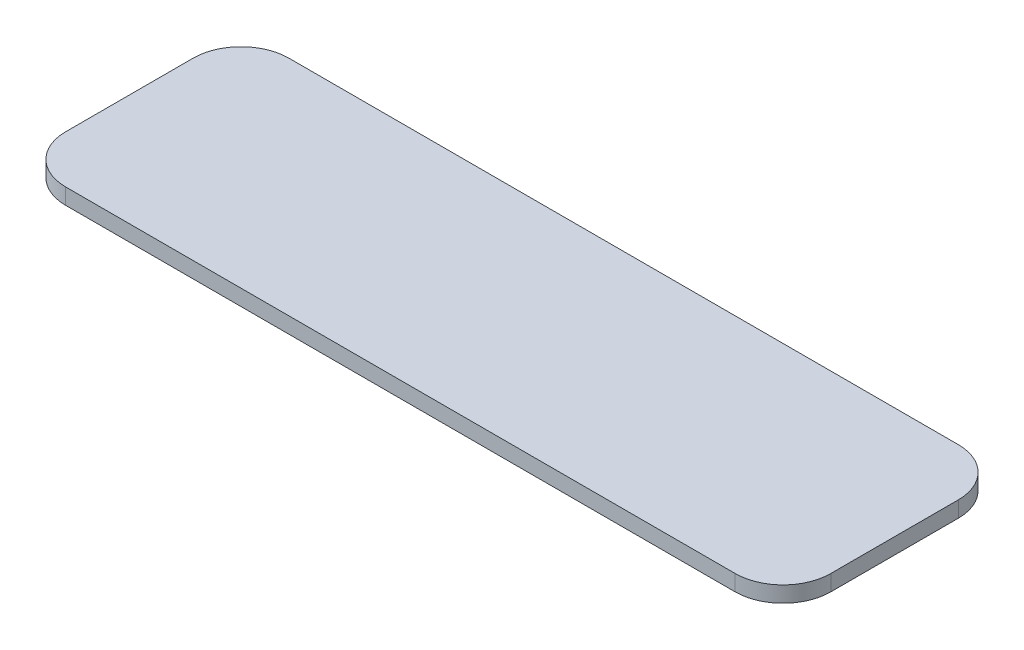
SolidWorks part; units mm, degrees
ref_plane "前视基准面" through (0, 0, 0) normal (0, 0, 1) x (1, 0, 0)
ref_plane "上视基准面" through (0, 0, 0) normal (0, 1, 0) x (1, 0, 0)
ref_plane "右视基准面" through (0, 0, 0) normal (1, 0, 0) x (0, 0, -1)
other "Configuration Table"
sketch "草图1" plane through (0, 0, 0) normal (0, 1, 0) x (1, 0, 0)
  line L1 (-31.5, 10.5) -> (31.5, 10.5)
  line L2 (-36, 6) -> (-36, -6)
  line L3 (-31.5, -10.5) -> (31.5, -10.5)
  line L4 (36, 6) -> (36, -6)
  line L5 (-36, 10.5) -> (36, -10.5) construction
  line L6 (-36, -10.5) -> (36, 10.5) construction
  arc A0 (31.5, 10.5) -> (36, 6) centre (31.5, 6) cw
  arc A1 (31.5, -10.5) -> (36, -6) centre (31.5, -6) ccw
  arc A2 (-36, -6) -> (-31.5, -10.5) centre (-31.5, -6) ccw
  arc A3 (-31.5, 10.5) -> (-36, 6) centre (-31.5, 6) ccw
  point P0 (0, 0)
  dimension "D3" = 4.5
  dimension "D1" = 21
  dimension "D2" = 72
extrude "凸台-拉伸1" add sketch "草图1" along normal blind 1.5
